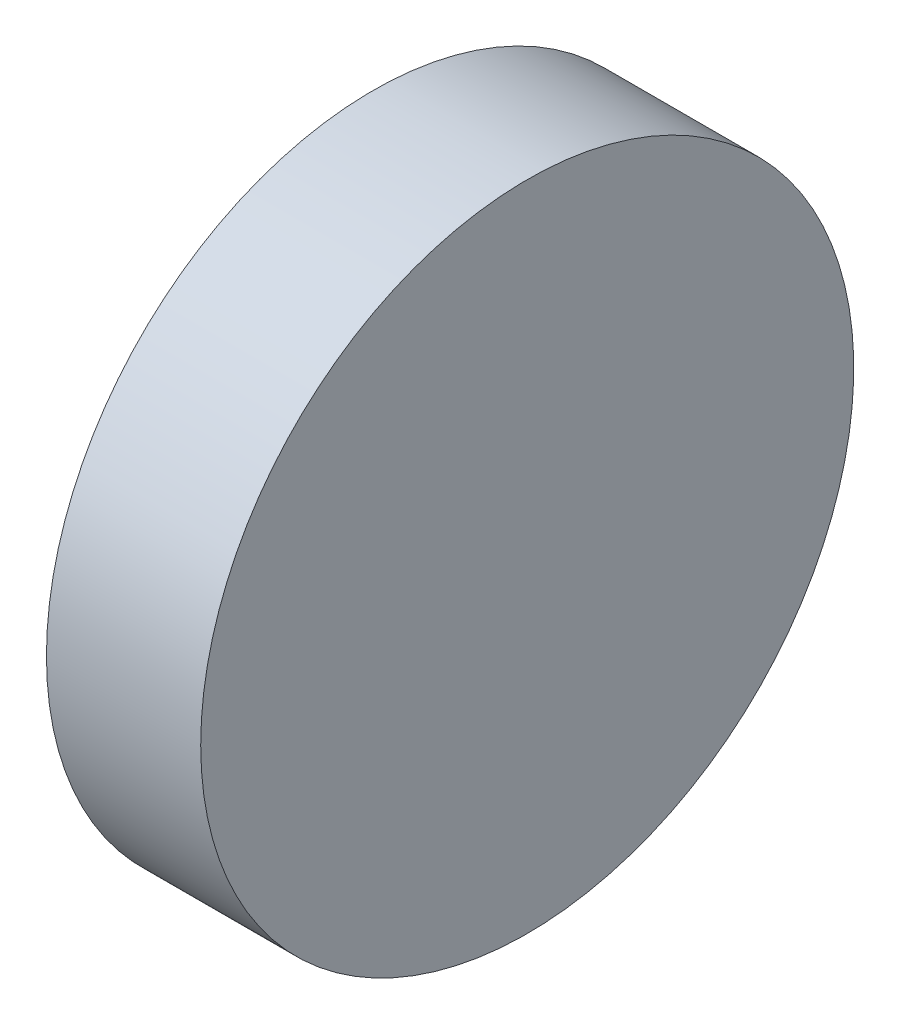
SolidWorks part; units mm, degrees
ref_plane "前视基准面" through (0, 0, 0) normal (0, 0, 1) x (1, 0, 0)
ref_plane "上视基准面" through (0, 0, 0) normal (0, 1, 0) x (1, 0, 0)
ref_plane "右视基准面" through (0, 0, 0) normal (1, 0, 0) x (0, 0, -1)
sketch "草图1" plane through (0, 0, 0) normal (0, 0, 1) x (1, 0, 0)
  line L0 (254.0008, 77.2932) -> (270.031, 77.2932) construction
  line L1 (259.7244, 77.2932) -> (259.7244, 89.9932)
  line L2 (265.7244, 77.2932) -> (265.7244, 89.9932)
  line L3 (259.7244, 77.2932) -> (265.7244, 77.2932)
  line L4 (259.7244, 89.9932) -> (265.7244, 89.9932)
  dimension "D1" = 6
revolve "旋转1" add sketch "草图1" angle 360 about L0
